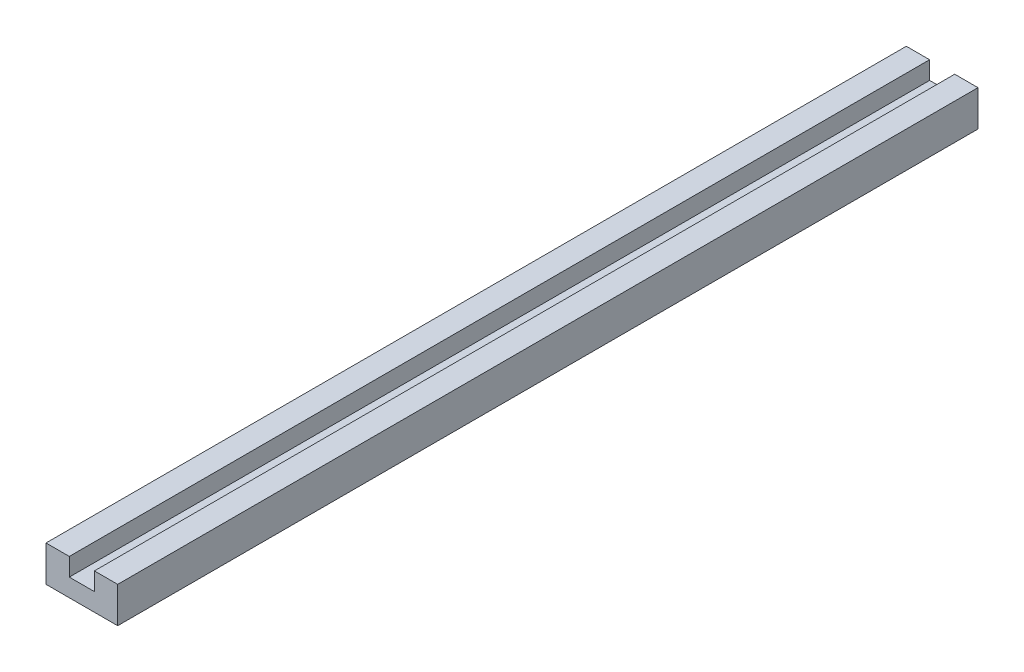
SolidWorks part; units mm, degrees
ref_plane "Front Plane" through (0, 0, 0) normal (0, 0, 1) x (1, 0, 0)
ref_plane "Top Plane" through (0, 0, 0) normal (0, 1, 0) x (1, 0, 0)
ref_plane "Right Plane" through (0, 0, 0) normal (1, 0, 0) x (0, 0, -1)
sketch "Sketch2" plane through (0, 0, 0) normal (0, 0, 1) x (1, 0, 0)
  line L1 (0, 0) -> (20, 0)
  line L2 (0, 0) -> (0, 10)
  line L3 (0, 10) -> (20, 10)
  line L4 (20, 0) -> (20, 10)
  dimension "D1" = 20
  dimension "D2" = 10
extrude "Boss-Extrude1" add sketch "Sketch2" along normal blind 240
sketch "Sketch4" plane through (0, 0, 240) normal (0, 0, 1) x (1, 0, 0)
  line L0 (20, 10) -> (0, 10) construction
  line L1 (6.5, 10) -> (13.5, 10)
  line L2 (6.5, 10) -> (6.5, 5)
  line L3 (6.5, 5) -> (13.5, 5)
  line L4 (13.5, 10) -> (13.5, 5)
  line L6 (6.5, 10) -> (0, 10)
  line L7 (13.5, 10) -> (20, 10)
  line M10 (20, 10) -> (0, 10)
  dimension "D1" = 7
  dimension "D2" = 5
extrude "Cut-Extrude1" cut sketch "Sketch4" against normal through all contours L4 L2 L3 M10
